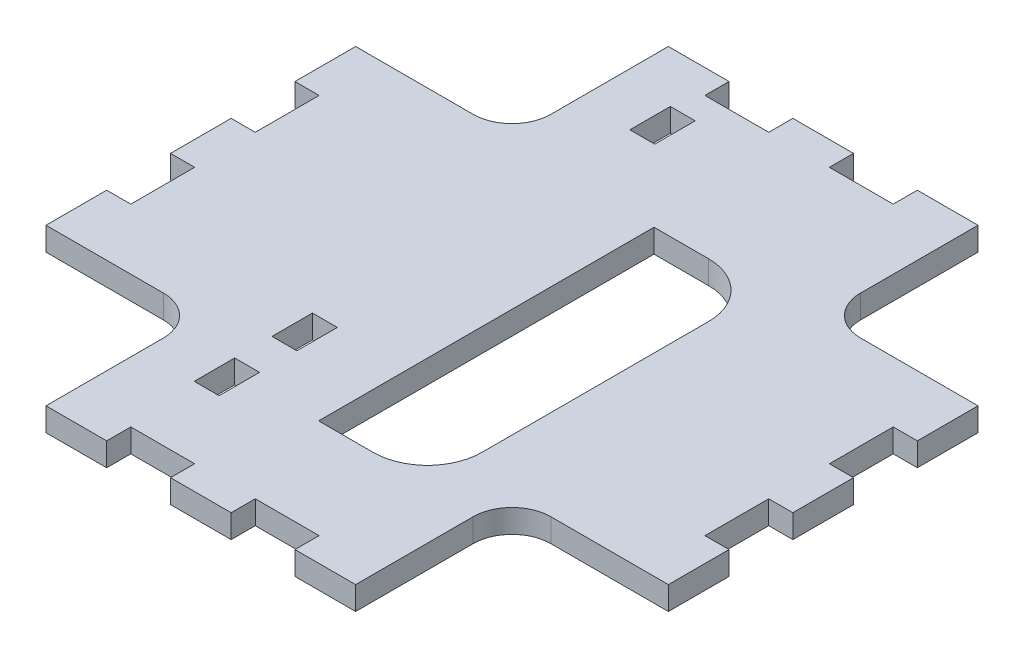
SolidWorks part; units mm, degrees
ref_plane "Front Plane" through (0, 0, 0) normal (0, 0, 1) x (1, 0, 0)
ref_plane "Top Plane" through (0, 0, 0) normal (0, 1, 0) x (1, 0, 0)
ref_plane "Right Plane" through (0, 0, 0) normal (1, 0, 0) x (0, 0, -1)
sketch "Sketch1" plane through (0, 0, 0) normal (0, 1, 0) x (1, 0, 0)
  line L0 (80, 0) -> (80, 80) construction
  line L1 (0, 0) -> (80, 0)
  line L2 (0, 0) -> (0, 80)
  line L3 (0, 80) -> (80, 80)
  line L4 (80, 0) -> (80, 80)
  line L5 (80, 80) -> (0, 80) construction
  line L7 (39.3, 15.8432) -> (48.3, 15.8432)
  line L8 (39.3, 15.8432) -> (39.3, 58.9568)
  line L9 (39.3, 58.9568) -> (48.3, 58.9568)
  line L10 (48.3, 15.8432) -> (48.3, 58.9568)
  line L12 (45.3, 15.8432) -> (45.3, 58.9568) construction
  line L13 (42.3, 58.9568) -> (42.3, 15.8432) construction
  line L14 (45.3, 16.4) -> (45.3, 58.4) construction
  line L15 (42.3, 16.4) -> (42.3, 58.4) construction
  line L17 (45.3, 37.4) -> (48.3, 37.4) construction
  line L18 (42.3, 40) -> (39.3, 40) construction
  line L20 (42.3, 37.4) -> (39.3, 37.4) construction
sketch "Sketch2" plane through (0, 0, 0) normal (0, 0, 1) x (1, 0, 0)
  line L1 (0, 0) -> (80, 0)
  line L2 (0, 0) -> (0, -3)
  line L3 (0, -3) -> (80, -3)
  line L4 (80, 0) -> (80, -3)
extrude "Boss-Extrude1" add sketch "Sketch1" against normal up to vertex (3 mm away) up to point (0, -3, 0)
sketch "Sketch3" plane through (0, 0, 0) normal (0, 1, 0) x (1, 0, 0)
  line L8 (36, 3) -> (28, 3)
  line L9 (28, 3) -> (28, 0)
  line L10 (28, 0) -> (36, 0)
  line L11 (36, 0) -> (36, 3)
  line L12 (36, 3) -> (28, 3) construction
  line L13 (28, 3) -> (28, 0) construction
  line L14 (28, 0) -> (36, 0) construction
  line L15 (36, 0) -> (36, 3) construction
  line L16 (77, 28) -> (80, 28)
  line L17 (77, 36) -> (77, 28)
  line L18 (80, 36) -> (77, 36)
  line L19 (80, 28) -> (80, 36)
  line L20 (77, 28) -> (80, 28) construction
  line L21 (77, 36) -> (77, 28) construction
  line L22 (80, 36) -> (77, 36) construction
  line L23 (80, 28) -> (80, 36) construction
  line L24 (44, 3) -> (44, 0)
  line L25 (52, 3) -> (44, 3)
  line L26 (52, 0) -> (52, 3)
  line L27 (44, 0) -> (52, 0)
  line L28 (44, 3) -> (44, 0) construction
  line L29 (52, 3) -> (44, 3) construction
  line L30 (52, 0) -> (52, 3) construction
  line L31 (44, 0) -> (52, 0) construction
  line L32 (0, 28) -> (3, 28)
  line L33 (0, 36) -> (0, 28)
  line L34 (3, 36) -> (0, 36)
  line L35 (3, 28) -> (3, 36)
  line L36 (0, 28) -> (3, 28) construction
  line L37 (0, 36) -> (0, 28) construction
  line L38 (3, 36) -> (0, 36) construction
  line L39 (3, 28) -> (3, 36) construction
  line L40 (20, 20) -> (0, 20)
  line L41 (0, 20) -> (0, 0)
  line L42 (0, 0) -> (20, 0)
  line L43 (20, 0) -> (20, 20)
  line L44 (20, 20) -> (0, 20) construction
  line L45 (0, 20) -> (0, 0) construction
  line L46 (0, 0) -> (20, 0) construction
  line L47 (20, 0) -> (20, 20) construction
  line L48 (60, 20) -> (60, 0)
  line L49 (80, 20) -> (60, 20)
  line L50 (80, 0) -> (80, 20)
  line L51 (60, 0) -> (80, 0)
  line L52 (60, 20) -> (60, 0) construction
  line L53 (80, 20) -> (60, 20) construction
  line L54 (80, 0) -> (80, 20) construction
  line L55 (60, 0) -> (80, 0) construction
  line L56 (36, 77) -> (36, 80)
  line L57 (28, 77) -> (36, 77)
  line L58 (28, 80) -> (28, 77)
  line L59 (36, 80) -> (28, 80)
  line L60 (36, 77) -> (36, 80) construction
  line L61 (28, 77) -> (36, 77) construction
  line L62 (28, 80) -> (28, 77) construction
  line L63 (36, 80) -> (28, 80) construction
  line L64 (0, 52) -> (0, 44)
  line L65 (0, 44) -> (3, 44)
  line L66 (3, 44) -> (3, 52)
  line L67 (3, 52) -> (0, 52)
  line L68 (0, 52) -> (0, 44) construction
  line L69 (0, 44) -> (3, 44) construction
  line L70 (3, 44) -> (3, 52) construction
  line L71 (3, 52) -> (0, 52) construction
  line L72 (20, 60) -> (20, 80)
  line L73 (0, 60) -> (20, 60)
  line L74 (0, 80) -> (0, 60)
  line L75 (20, 80) -> (0, 80)
  line L76 (20, 60) -> (20, 80) construction
  line L77 (0, 60) -> (20, 60) construction
  line L78 (0, 80) -> (0, 60) construction
  line L79 (20, 80) -> (0, 80) construction
  line L80 (80, 52) -> (77, 52)
  line L81 (80, 44) -> (80, 52)
  line L82 (77, 44) -> (80, 44)
  line L83 (77, 52) -> (77, 44)
  line L84 (80, 52) -> (77, 52) construction
  line L85 (80, 44) -> (80, 52) construction
  line L86 (77, 44) -> (80, 44) construction
  line L87 (77, 52) -> (77, 44) construction
  line L88 (80, 80) -> (60, 80)
  line L89 (80, 60) -> (80, 80)
  line L90 (60, 60) -> (80, 60)
  line L91 (60, 80) -> (60, 60)
  line L92 (80, 80) -> (60, 80) construction
  line L93 (80, 60) -> (80, 80) construction
  line L94 (60, 60) -> (80, 60) construction
  line L95 (60, 80) -> (60, 60) construction
  line L96 (52, 77) -> (52, 80)
  line L97 (44, 77) -> (52, 77)
  line L98 (44, 80) -> (44, 77)
  line L99 (52, 80) -> (44, 80)
  line L144 (52, 77) -> (52, 80) construction
  line L145 (44, 77) -> (52, 77) construction
  line L146 (44, 80) -> (44, 77) construction
  line L147 (52, 80) -> (44, 80) construction
  line L148 (30, 17.35) -> (27, 17.35)
  line L149 (27, 17.35) -> (27, 12.35)
  line L150 (27, 12.35) -> (30, 12.35)
  line L151 (30, 12.35) -> (30, 17.35)
  line L152 (30, 17.35) -> (27, 17.35) construction
  line L153 (27, 17.35) -> (27, 12.35) construction
  line L154 (27, 12.35) -> (30, 12.35) construction
  line L155 (30, 12.35) -> (30, 17.35) construction
  line L156 (30, 22.35) -> (30, 27.35)
  line L157 (30, 27.35) -> (27, 27.35)
  line L158 (27, 27.35) -> (27, 22.35)
  line L159 (27, 22.35) -> (30, 22.35)
  line L160 (30, 22.35) -> (30, 27.35) construction
  line L161 (30, 27.35) -> (27, 27.35) construction
  line L162 (27, 27.35) -> (27, 22.35) construction
  line L163 (27, 22.35) -> (30, 22.35) construction
  line L164 (27, 68.35) -> (30, 68.35)
  line L165 (30, 68.35) -> (30, 73.35)
  line L166 (30, 73.35) -> (27, 73.35)
  line L167 (27, 73.35) -> (27, 68.35)
  line L168 (27, 68.35) -> (30, 68.35) construction
  line L169 (30, 68.35) -> (30, 73.35) construction
  line L170 (30, 73.35) -> (27, 73.35) construction
  line L171 (27, 73.35) -> (27, 68.35) construction
  line L564 (36.1, 3.1) -> (27.9, 3.1)
  line L565 (27.9, 3.1) -> (27.9, -0.1)
  line L566 (27.9, -0.1) -> (36.1, -0.1)
  line L567 (36.1, -0.1) -> (36.1, 3.1)
  line L568 (76.9, 27.9) -> (80.1, 27.9)
  line L569 (80.1, 27.9) -> (80.1, 36.1)
  line L570 (80.1, 36.1) -> (76.9, 36.1)
  line L571 (76.9, 36.1) -> (76.9, 27.9)
  line L572 (43.9, 3.1) -> (43.9, -0.1)
  line L573 (43.9, -0.1) -> (52.1, -0.1)
  line L574 (52.1, -0.1) -> (52.1, 3.1)
  line L575 (52.1, 3.1) -> (43.9, 3.1)
  line L576 (-0.1, 27.9) -> (3.1, 27.9)
  line L577 (3.1, 27.9) -> (3.1, 36.1)
  line L578 (3.1, 36.1) -> (-0.1, 36.1)
  line L579 (-0.1, 36.1) -> (-0.1, 27.9)
  line L580 (20.1, 20.1) -> (-0.1, 20.1)
  line L581 (-0.1, 20.1) -> (-0.1, -0.1)
  line L582 (-0.1, -0.1) -> (20.1, -0.1)
  line L583 (20.1, -0.1) -> (20.1, 20.1)
  line L584 (59.9, 20.1) -> (59.9, -0.1)
  line L585 (59.9, -0.1) -> (80.1, -0.1)
  line L586 (80.1, -0.1) -> (80.1, 20.1)
  line L587 (80.1, 20.1) -> (59.9, 20.1)
  line L588 (36.1, 76.9) -> (36.1, 80.1)
  line L589 (36.1, 80.1) -> (27.9, 80.1)
  line L590 (27.9, 80.1) -> (27.9, 76.9)
  line L591 (27.9, 76.9) -> (36.1, 76.9)
  line L592 (-0.1, 52.1) -> (-0.1, 43.9)
  line L593 (-0.1, 43.9) -> (3.1, 43.9)
  line L594 (3.1, 43.9) -> (3.1, 52.1)
  line L595 (3.1, 52.1) -> (-0.1, 52.1)
  line L596 (20.1, 59.9) -> (20.1, 80.1)
  line L597 (20.1, 80.1) -> (-0.1, 80.1)
  line L598 (-0.1, 80.1) -> (-0.1, 59.9)
  line L599 (-0.1, 59.9) -> (20.1, 59.9)
  line L600 (80.1, 52.1) -> (76.9, 52.1)
  line L601 (76.9, 52.1) -> (76.9, 43.9)
  line L602 (76.9, 43.9) -> (80.1, 43.9)
  line L603 (80.1, 43.9) -> (80.1, 52.1)
  line L604 (80.1, 80.1) -> (59.9, 80.1)
  line L605 (59.9, 80.1) -> (59.9, 59.9)
  line L606 (59.9, 59.9) -> (80.1, 59.9)
  line L607 (80.1, 59.9) -> (80.1, 80.1)
  line L608 (52.1, 76.9) -> (52.1, 80.1)
  line L609 (52.1, 80.1) -> (43.9, 80.1)
  line L610 (43.9, 80.1) -> (43.9, 76.9)
  line L611 (43.9, 76.9) -> (52.1, 76.9)
  line L612 (30.1, 17.45) -> (26.9, 17.45)
  line L613 (26.9, 17.45) -> (26.9, 12.25)
  line L614 (26.9, 12.25) -> (30.1, 12.25)
  line L615 (30.1, 12.25) -> (30.1, 17.45)
  line L616 (30.1, 22.25) -> (30.1, 27.45)
  line L617 (30.1, 27.45) -> (26.9, 27.45)
  line L618 (26.9, 27.45) -> (26.9, 22.25)
  line L619 (26.9, 22.25) -> (30.1, 22.25)
  line L620 (26.9, 68.25) -> (30.1, 68.25)
  line L621 (30.1, 68.25) -> (30.1, 73.45)
  line L622 (30.1, 73.45) -> (26.9, 73.45)
  line L623 (26.9, 73.45) -> (26.9, 68.25)
  dimension "D1" = 0
  dimension "D2" = 0
  dimension "D3" = 0
  dimension "D4" = 0
  dimension "D5" = 0
  dimension "D6" = 0
  dimension "D7" = 0
  dimension "D8" = 0
  dimension "D9" = 0
  dimension "D10" = 0
  dimension "D11" = 0
  dimension "D12" = 0
  dimension "D13" = 0
  dimension "D14" = 0
  dimension "D15" = 0
  dimension "D16" = 0.1
extrude "Cut-Extrude1" cut sketch "Sketch3" against normal through all
fillet "Fillet1" radius 5 4 edges at (20.1, -1.5, -20.1) (20.1, -1.5, -59.9) (59.9, -1.5, -59.9) (59.9, -1.5, -20.1)
sketch "Sketch4" plane through (0, 0, 0) normal (0, 1, 0) x (1, 0, 0)
  line L0 (48.3, 15.8432) -> (53.3, 15.8432)
  line L1 (53.3, 15.8432) -> (53.3, 58.9568)
  line L2 (53.3, 58.9568) -> (48.3, 58.9568)
  line L3 (48.3, 15.8432) -> (48.3, 58.9568) construction
  line L4 (48.3, 15.8432) -> (48.3, 58.9568)
  dimension "D1" = 5
extrude "Cut-Extrude2" cut sketch "Sketch4" against normal through all
fillet "Fillet2" radius 7 2 edges at (53.3, -1.5, -15.8432) (53.3, -1.5, -58.9568)
